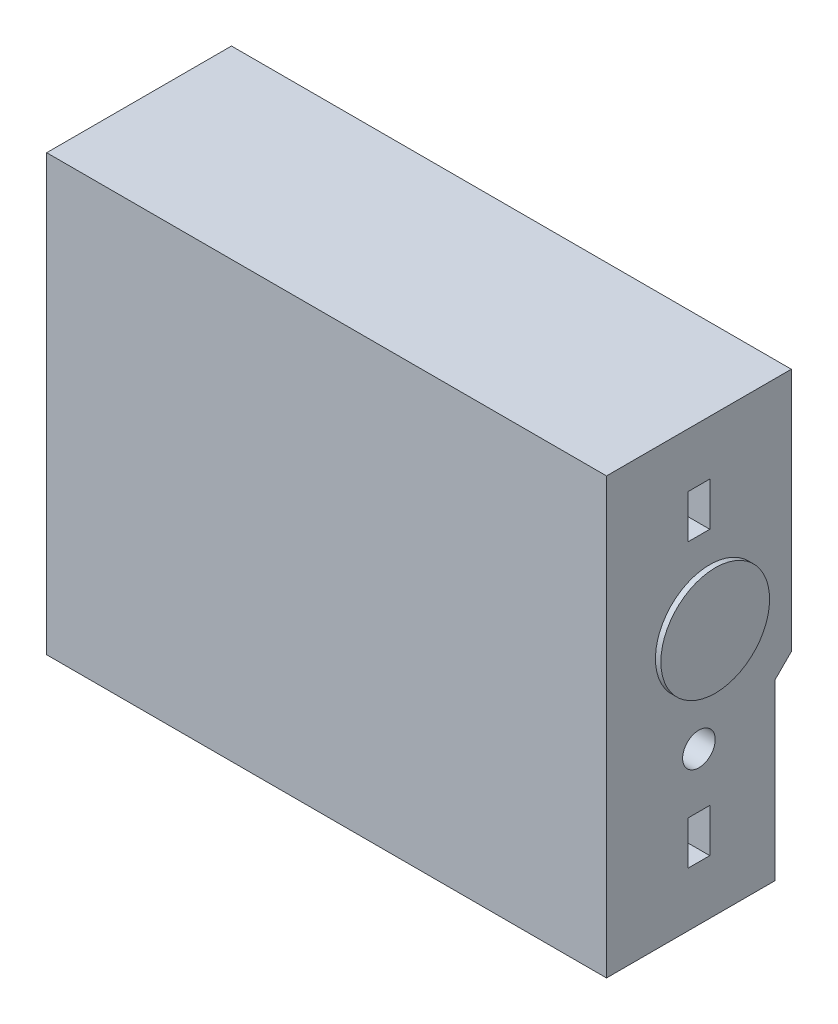
SolidWorks part; units mm, degrees
ref_plane "Plan de face" through (0, 0, 0) normal (0, 0, 1) x (1, 0, 0)
ref_plane "Plan de dessus" through (0, 0, 0) normal (0, 1, 0) x (1, 0, 0)
ref_plane "Plan de droite" through (0, 0, 0) normal (1, 0, 0) x (0, 0, -1)
sketch "Esquisse1" plane through (0, 0, 0) normal (0, 0, 1) x (1, 0, 0)
  line L0 (0, 0) -> (0, 88.5433) construction
  line L1 (0, 88.5433) -> (0, -74.4734) construction
  line L2 (0, -74.4734) -> (0, 0) construction
  line L3 (0, 0) -> (166.5595, 0) construction
  line L4 (166.5595, 0) -> (-164.8106, 0) construction
  line L6 (-51.5, 40) -> (51.5, 40)
  line L7 (-51.5, 40) -> (-51.5, -40)
  line L8 (-51.5, -40) -> (51.5, -40)
  line L9 (51.5, 40) -> (51.5, -40)
  line L10 (-51.5, 40) -> (51.5, -40) construction
  line L11 (-51.5, -40) -> (51.5, 40) construction
  dimension "D1" = 103
  dimension "D2" = 80
extrude "Boss.-Extru.1" add sketch "Esquisse1" along normal blind 34
sketch "Esquisse2" plane through (-51.5, 0, 0) normal (-1, 0, 0) x (0, 0, 1)
  line L0 (0, -5) -> (0, -40)
  line L1 (0, -5) -> (3, -5)
  line L2 (0, 40) -> (0, -40) construction
  line L3 (3, -5) -> (3, -8)
  line L4 (3, -8) -> (0, -5)
  line L5 (3, -8) -> (3, -40)
  line L6 (34, -40) -> (0, -40) construction
  line L7 (3, -40) -> (6, -40)
  line L8 (6, -40) -> (3, -37)
  line L9 (3, -37) -> (3, -40)
  line L10 (0, -40) -> (3, -40)
  line L11 (3, -8) -> (0, -5)
  dimension "D1" = 3
  dimension "D2" = 3
  dimension "D3" = 3
  dimension "D4" = 35
extrude "Enlèv. mat.-Extru.2" cut sketch "Esquisse2" against normal blind 224 contours L5 L4 L8 L9
sketch "Esquisse3" plane through (0, 0, 0) normal (0, 0, -1) x (-1, 0, 0)
  line L0 (0, 0) -> (0, 40) construction
  line L1 (-51.5, 40) -> (51.5, 40) construction
  line L2 (-51.5, -5) -> (-51.5, 40) construction
  line L3 (-31.7301, 27.5) -> (31.7301, 27.5)
  line L4 (-31.7301, 27.5) -> (-31.7301, 7.5)
  line L5 (-31.7301, 7.5) -> (31.7301, 7.5)
  line L6 (31.7301, 27.5) -> (31.7301, 7.5)
  line L7 (-31.7301, 27.5) -> (31.7301, 7.5) construction
  line L8 (-31.7301, 7.5) -> (31.7301, 27.5) construction
  point P5 (0, 17.5)
  point P12 (-31.7301, 17.5)
  dimension "D1" = 19.7699
  dimension "D2" = 22.5
  dimension "D3" = 20
extrude "Enlèv. mat.-Extru.3" cut sketch "Esquisse3" against normal blind 1
sketch "Esquisse4" plane through (0, 0, 3) normal (0, 0, -1) x (-1, 0, 0)
  line L0 (0, 0) -> (0, -40) construction
  line L1 (-51.5, -40) -> (51.5, -40) construction
  line L2 (0, -40) -> (0, -20) construction
  line L3 (0, -20) -> (-49.6645, -20) construction
  line L4 (-49.6645, -20) -> (44.9952, -20) construction
  circle A0 centre (-7.5, -20) radius 4
  circle A1 centre (-22.5, -20) radius 4
  circle A2 centre (7.5, -20) radius 4
  circle A3 centre (22.5, -20) radius 4
  dimension "D1" = 8
  dimension "D2" = 8
  dimension "D3" = 8
  dimension "D4" = 8
  dimension "D5" = 15
  dimension "D6" = 7.5
  dimension "D7" = 15
  dimension "D8" = 15
extrude "Boss.-Extru.2" add sketch "Esquisse4" along normal blind 1
sketch "Esquisse5" plane through (51.5, 0, 0) normal (1, 0, 0) x (0, 0, -1)
  line L1 (-17, 40) -> (-17, -40) construction
  line L2 (-34, 40) -> (0, 40) construction
  line L3 (-34, -40) -> (-3, -40) construction
  line L4 (-19, 30) -> (-15, 30)
  line L5 (-19, 30) -> (-19, 22)
  line L6 (-19, 22) -> (-15, 22)
  line L7 (-15, 30) -> (-15, 22)
  line L8 (-19, 30) -> (-15, 22) construction
  line L9 (-19, 22) -> (-15, 30) construction
  line L10 (-19, -30) -> (-15, -30)
  line L11 (-19, -30) -> (-19, -22)
  line L12 (-19, -22) -> (-15, -22)
  line L13 (-15, -30) -> (-15, -22)
  line L14 (-19, -30) -> (-15, -22) construction
  line L15 (-19, -22) -> (-15, -30) construction
  circle A0 centre (-17, -12) radius 3
  point P0 (-17, 26)
  point P12 (-17, -26)
  dimension "D1" = 6
  dimension "D8" = 10
  dimension "D2" = 8
  dimension "D3" = 4
  dimension "D4" = 4
  dimension "D5" = 8
  dimension "D6" = 10
  dimension "D7" = 10
extrude "Enlèv. mat.-Extru.4" cut sketch "Esquisse5" against normal blind 5
sketch "Esquisse6" plane through (51.5, 0, 0) normal (1, 0, 0) x (0, 0, -1)
  line L0 (0, -5) -> (0, 40) construction
  circle A0 centre (-15, 6.3672) radius 10
  dimension "D1" = 20
  dimension "D2" = 15
extrude "Boss.-Extru.3" add sketch "Esquisse6" along normal blind 1
sketch "Esquisse7" plane through (-51.5, 0, 0) normal (-1, 0, 0) x (0, 0, 1)
  line L0 (17, 40) -> (18.5, -40) construction
  line L1 (34, 40) -> (0, 40) construction
  line L2 (34, -40) -> (3, -40) construction
  line L4 (14.1061, -9.9928) -> (22.1061, -9.9928)
  line L5 (14.1061, -9.9928) -> (14.1061, -27.9928)
  line L6 (14.1061, -27.9928) -> (22.1061, -27.9928)
  line L7 (22.1061, -9.9928) -> (22.1061, -27.9928)
  line L8 (14.1061, -9.9928) -> (22.1061, -27.9928) construction
  line L9 (14.1061, -27.9928) -> (22.1061, -9.9928) construction
  line L10 (17.2127, 28.6546) -> (21.2127, 28.6546)
  line L11 (17.2127, 28.6546) -> (17.2127, 16.6546)
  line L12 (17.2127, 16.6546) -> (21.2127, 16.6546)
  line L13 (21.2127, 28.6546) -> (21.2127, 16.6546)
  point P6 (18.1061, -18.9928)
  dimension "D1" = 4
  dimension "D2" = 8
  dimension "12" = 12
  dimension "D3" = 18
extrude "Enlèv. mat.-Extru.5" cut sketch "Esquisse7" against normal blind 5
